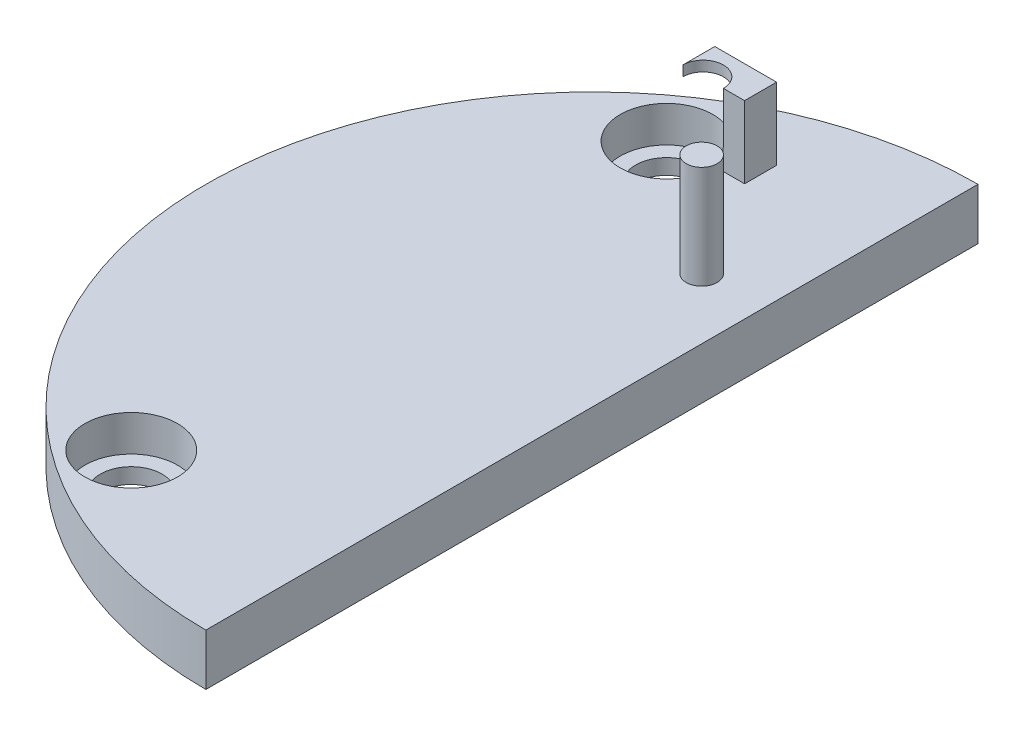
SolidWorks part; units mm, degrees
ref_plane "Ebene vorne" through (0, 0, 0) normal (0, 0, 1) x (1, 0, 0)
ref_plane "Ebene oben" through (0, 0, 0) normal (0, 1, 0) x (1, 0, 0)
ref_plane "Ebene rechts" through (0, 0, 0) normal (1, 0, 0) x (0, 0, -1)
sketch "Skizze1" plane through (0, 0, 0) normal (0, 1, 0) x (1, 0, 0)
  line L0 (0, 0) -> (0, -75)
  line L1 (0, -37.5) -> (-48.465, -37.5) construction
  arc A1 (0, -75) -> (0, 0) centre (0, -37.5) cw
  dimension "D1" = 75
extrude "Aufsatz-Linear austragen1" add sketch "Skizze1" along normal blind 5
sketch "Skizze11" plane through (0, 5, 0) normal (0, 1, 0) x (1, 0, 0)
  line L0 (0, -37.5) -> (-37.5, -37.5) construction
  line L1 (0, -75) -> (0, 0) construction
  line L2 (-18.75, -37.5) -> (-18.75, -1.2821) construction
  line L3 (-18.75, -1.2821) -> (-18.75, -74.2151) construction
  arc A0 (0, 0) -> (0, -75) centre (0, -37.5) ccw construction
  circle A1 centre (-18.75, -11.5) radius 4.5
  circle A2 centre (-18.75, -63.5) radius 4.5
  dimension "D1" = 52
  dimension "D2" = 9
extrude "Schnitt-Linear austragen1" cut sketch "Skizze11" against normal blind 3.5
sketch "Skizze12" plane through (0, 1.5, 0) normal (0, 1, 0) x (1, 0, 0)
  circle A0 centre (-18.75, -63.5) radius 3
  circle A1 centre (-18.75, -11.5) radius 3
extrude "Schnitt-Linear austragen2" cut sketch "Skizze12" against normal blind 1.5
sketch "Skizze13" plane through (0, 5, 0) normal (0, 1, 0) x (1, 0, 0)
  line L0 (-13.4591, -11.2984) -> (-11.3733, -11.2984)
  line L1 (-11.3733, -8.1916) -> (-13.4591, -8.1916)
  line L2 (-13.4591, -8.1916) -> (-13.4591, -11.2984)
  line L3 (-11.3733, -8.1916) -> (-11.3733, -11.2984)
extrude "Aufsatz-Linear austragen2" add sketch "Skizze13" along normal blind 6
sketch "Skizze14" plane through (0, 11, 0) normal (0, 1, 0) x (1, 0, 0)
  line L0 (-11.3733, -8.1916) -> (-11.3733, -11.2984)
  line L1 (-11.3733, -11.2984) -> (-17.3733, -11.2984)
  line L2 (-17.3733, -11.2984) -> (-17.3733, -8.1916)
  line L3 (-17.3733, -8.1916) -> (-11.3733, -8.1916)
extrude "Aufsatz-Linear austragen3" add sketch "Skizze14" along normal blind 1
sketch "Skizze16" plane through (0, 12, 0) normal (0, 1, 0) x (1, 0, 0)
  line L0 (-17.3733, -11.2984) -> (-13.43, -11.2984)
  line L1 (-17.3733, -11.2984) -> (-11.3733, -11.2984) construction
  arc A0 (-13.43, -11.2984) -> (-17.3733, -11.2984) centre (-15.4017, -11.2984) ccw
extrude "Schnitt-Linear austragen3" cut sketch "Skizze16" against normal blind 5
sketch "Skizze17" plane through (0, 5, 0) normal (0, 1, 0) x (1, 0, 0)
  circle A0 centre (-5.9051, -20.9372) radius 1.5
extrude "Aufsatz-Linear austragen4" add sketch "Skizze17" along normal blind 10
